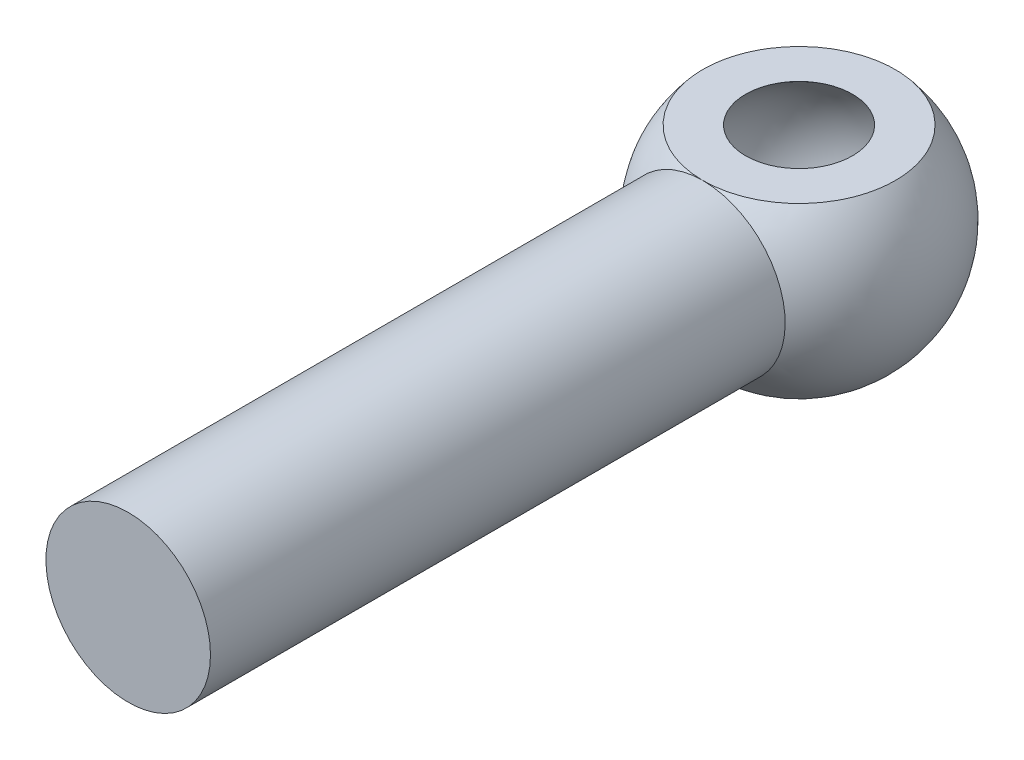
SolidWorks part; units mm, degrees
ref_plane "Front Plane" through (0, 0, 0) normal (0, 0, 1) x (1, 0, 0)
ref_plane "Top Plane" through (0, 0, 0) normal (0, 1, 0) x (1, 0, 0)
ref_plane "Right Plane" through (0, 0, 0) normal (1, 0, 0) x (0, 0, -1)
sketch "Sketch1" plane through (0, 0, 0) normal (0, 0, 1) x (1, 0, 0)
  circle A0 centre (0, 0) radius 1.651
extrude "Extrude1" add sketch "Sketch1" along normal blind 13.462
sketch "Sketch3" plane through (0, 0, 13.462) normal (0, 0, 1) x (1, 0, 0)
  line L0 (0, 0) -> (-1.651, 0) construction
  circle A0 centre (0, 0) radius 1.651 construction
sketch "Sketch4" plane through (0, 0, 0) normal (0, 0, -1) x (-1, 0, 0)
  line L0 (0, 0) -> (1.651, 0) construction
  circle A0 centre (0, 0) radius 1.651 construction
sketch "Sketch5" plane through (0, 0, 0) normal (0, 0, -1) x (-1, 0, 0)
  line L0 (0, 0) -> (0, 1.651) construction
  circle A0 centre (0, 0) radius 1.651 construction
ref_plane "Plane1" through (0, 0, 0) normal (0, 1, 0) x (-1, 0, 0)
ref_plane "Plane2" through (0, 1.651, 0) normal (0, 1, 0) x (-1, 0, 0)
sketch "Sketch2" plane through (0, 0, 0) normal (0, 0, -1) x (-1, 0, 0)
  line L0 (2.54, 0) -> (-2.54, 0)
  arc A0 (2.54, 0) -> (-2.54, 0) centre (0, 0) ccw
revolve "Revolve1" add sketch "Sketch2" angle 360 about L0
sketch "Sketch6" plane through (0, 1.651, 0) normal (0, 1, 0) x (-1, 0, 0)
  circle A0 centre (0, 0) radius 2.7829
extrude "Extrude2" cut sketch "Sketch6" along normal through all
sketch "Sketch7" plane through (0, 0, 0) normal (0, 1, 0) x (-1, 0, 0)
  line L0 (0, 1.9685) -> (0, -1.9685)
  arc A0 (0, -1.9685) -> (0, 1.9685) centre (0, 0) ccw
revolve "Cut-Revolve1" cut sketch "Sketch7" angle 360 about L0
